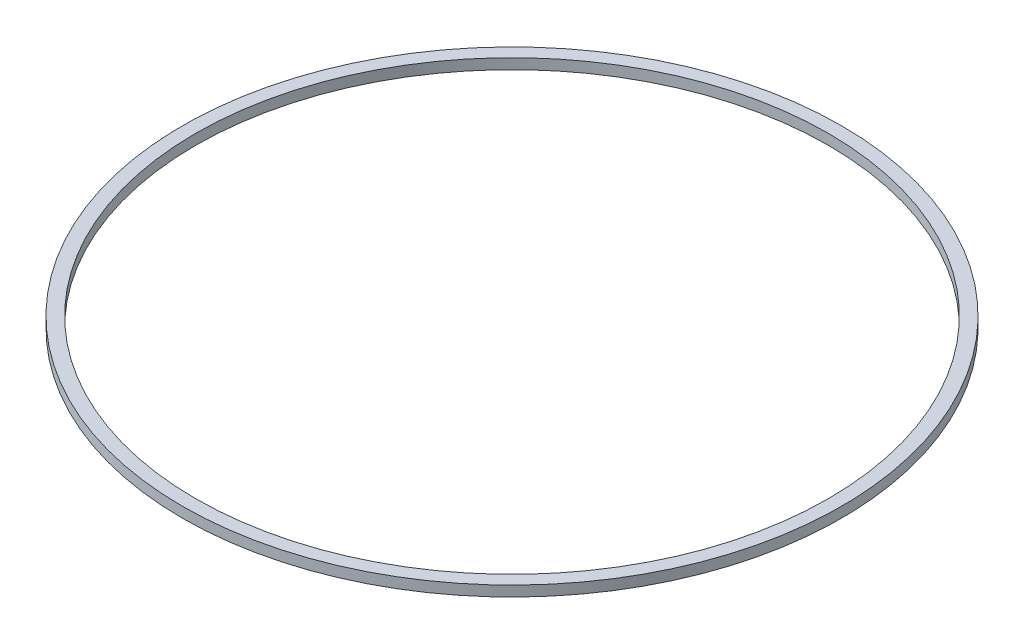
SolidWorks part; units mm, degrees
ref_plane "Front Plane" through (0, 0, 0) normal (0, 0, 1) x (1, 0, 0)
ref_plane "Top Plane" through (0, 0, 0) normal (0, 1, 0) x (1, 0, 0)
ref_plane "Right Plane" through (0, 0, 0) normal (1, 0, 0) x (0, 0, -1)
sketch "Sketch1" plane through (0, 0, 0) normal (0, 1, 0) x (1, 0, 0)
  circle A0 centre (0, 0) radius 60.96
  circle A1 centre (0, 0) radius 63.5
  dimension "D1" = 121.92
  dimension "D2" = 127
extrude "Boss-Extrude1" add sketch "Sketch1" along normal mid plane 2
